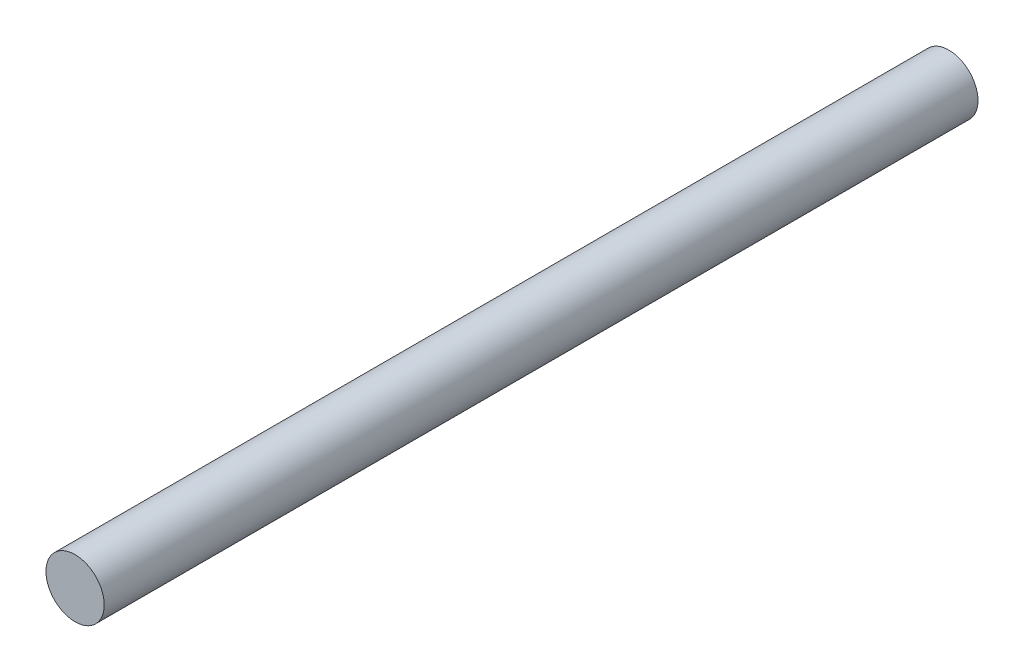
SolidWorks part; units mm, degrees
material "1023 Carbon Steel Sheet (SS)"
ref_plane "Front Plane" through (0, 0, 0) normal (0, 0, 1) x (1, 0, 0)
ref_plane "Top Plane" through (0, 0, 0) normal (0, 1, 0) x (1, 0, 0)
ref_plane "Right Plane" through (0, 0, 0) normal (1, 0, 0) x (0, 0, -1)
sketch "Sketch2" plane through (0, 0, 0) normal (0, 0, 1) x (1, 0, 0)
  circle A0 centre (0, 0) radius 6
  dimension "D1" = 12
extrude "Boss-Extrude1" add sketch "Sketch2" along normal mid plane 180
equation "\"tubeOutDiameter\" = 35mm"
equation "\"wheelShaftDiameter\"= 12mm"
equation "\"wheelThickness\"= 135mm"
equation "\"BearingDiameter\"= 20mm"
equation "\"BearingThickness\"= 10mm"
equation "\"frontShaftDiameter\"= 20mm"
equation "\"D1@Sketch2\"=\"wheelShaftDiameter\""
